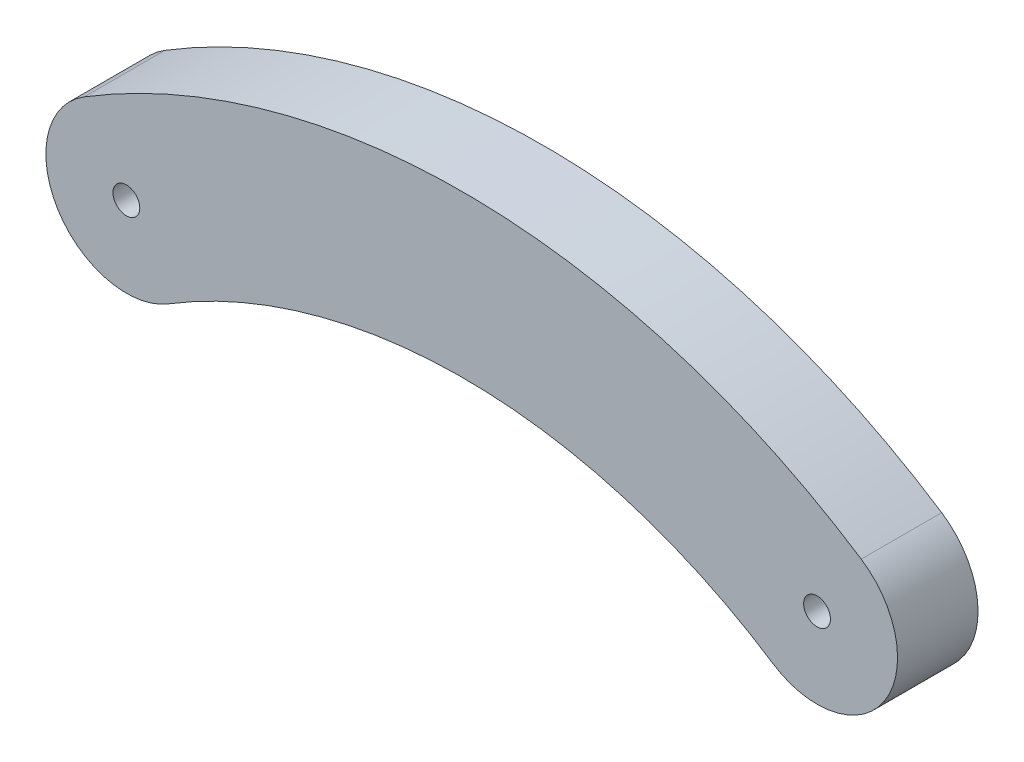
SolidWorks part; units mm, degrees
ref_plane "Front Plane" through (0, 0, 0) normal (0, 0, 1) x (1, 0, 0)
ref_plane "Top Plane" through (0, 0, 0) normal (0, 1, 0) x (1, 0, 0)
ref_plane "Right Plane" through (0, 0, 0) normal (1, 0, 0) x (0, 0, -1)
sketch "Sketch1" plane through (0, 0, 0) normal (0, 0, 1) x (1, 0, 0)
  arc A0 (-10.723, 0.9788) -> (15.0214, 0.5841) centre (1.8381, -19.5063) cw construction
  arc A1 (16.6673, 3.0923) -> (-12.2912, 3.5363) centre (1.8381, -19.5063) ccw
  arc A2 (13.3755, -1.9241) -> (-9.1548, -1.5787) centre (1.8381, -19.5063) ccw
  arc A3 (13.3755, -1.9241) -> (16.6673, 3.0923) centre (15.0214, 0.5841) ccw
  arc A4 (-12.2912, 3.5363) -> (-9.1548, -1.5787) centre (-10.723, 0.9788) ccw
  circle A5 centre (-10.723, 0.9788) radius 0.5
  circle A6 centre (15.0214, 0.5841) radius 0.5
  point P3 (2.2065, 4.5205)
  dimension "D2" = 6
  dimension "D3" = 1
  dimension "D1" = 25.7474
extrude "Boss-Extrude1" add sketch "Sketch1" along normal blind 3 contours A1 A4 A2 A3
